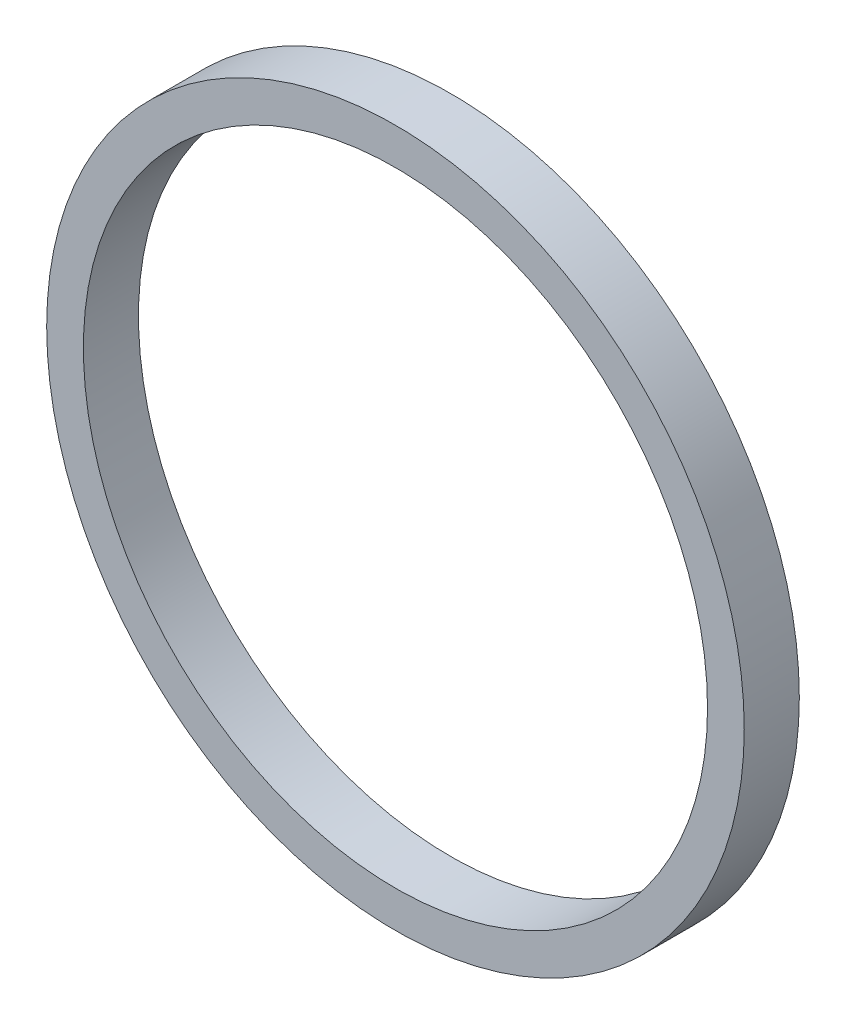
SolidWorks part; units mm, degrees
material "1060 Сплав"
ref_plane "Спереди" through (0, 0, 0) normal (0, 0, 1) x (1, 0, 0)
ref_plane "Сверху" through (0, 0, 0) normal (0, 1, 0) x (1, 0, 0)
ref_plane "Справа" through (0, 0, 0) normal (1, 0, 0) x (0, 0, -1)
sketch "Эскиз1" plane through (0, 0, 0) normal (0, 0, 1) x (1, 0, 0)
  circle A0 centre (0, 0) radius 8.5
  circle A1 centre (0, 0) radius 9.5
  dimension "D1" = 19
  dimension "D2" = 17
extrude "Бобышка-Вытянуть1" add sketch "Эскиз1" along normal blind 1.5
